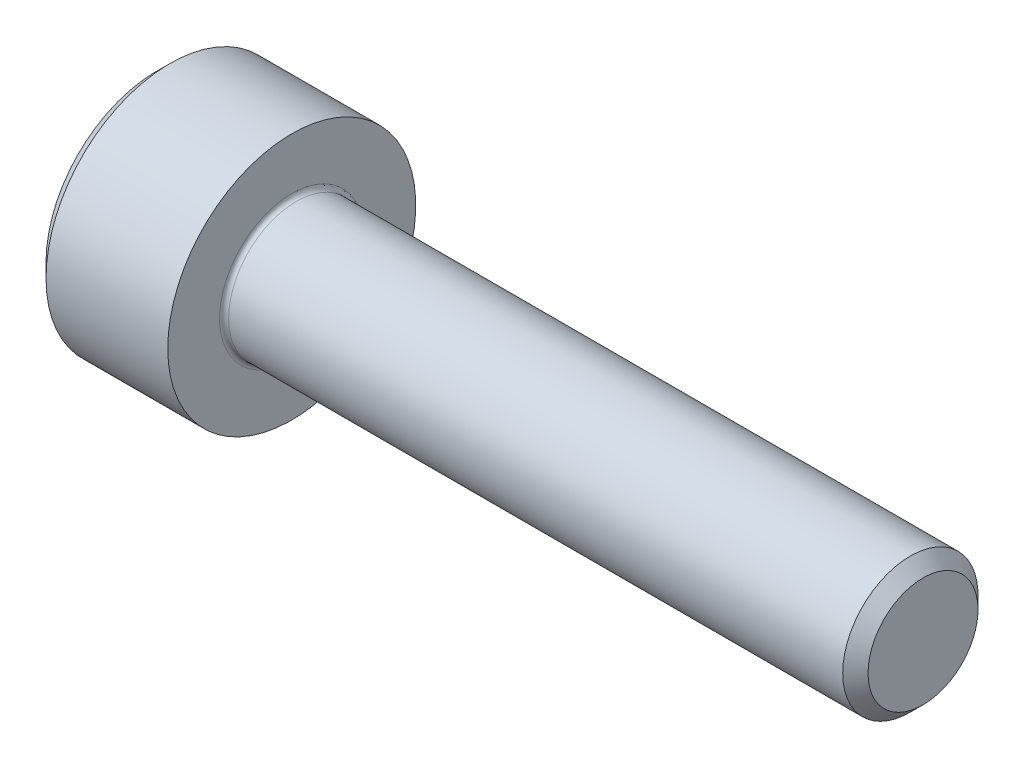
SolidWorks part; units mm, degrees
revolve "Base-Revolve" add sketch "BodySke"
sketch "BodySke" plane through (0, 0, 0) normal (0, 0, 1) x (1, 0, 0)
  line L0 (0, 0) -> (0, 2.45)
  line L1 (0.3, 2.75) -> (3, 2.75)
  line L2 (3, 2.75) -> (3, 1.5)
  line L3 (3, 1.5) -> (16.7195, 1.5)
  line L4 (17, 1.2195) -> (17, 0)
  line L5 (17, 0) -> (0, 0)
  line L6 (-31.75, 0) -> (127, 0) construction
  line L7 (0, 2.45) -> (0.3, 2.75)
  line L8 (17, 1.2195) -> (16.7195, 1.5)
  line L9 (0, -2.45) -> (0.3, -2.75) construction
  line L10 (17, -1.2195) -> (16.7195, -1.5) construction
  line L11 (3.5, 9.525) -> (3.5, 3.175) construction
  line L12 (3, 9.525) -> (3, 3.175) construction
  line L13 (-33, 9.525) -> (-33, 3.175) construction
  dimension "Diameter" = 3
  dimension "Head_ht" = 3
  dimension "Length" = 14
  dimension "Body_ch_ang" = 45
  dimension "Head_dia" = 5.5
  dimension "Head_ch_ang" = 45
  dimension "Minor_dia" = 2.439
  dimension "Advance" = 0.5
  dimension "Thread_nom" = 14
  dimension "Thread_length" = 50
  dimension "Head_ch_ht" = 0.3
cosmetic thread "ThreadCosmetic" [suppressed]
fillet "Fillet1" radius 0.1 1 edges at (3, 0, 1.5)
material "Plain Carbon Steel"
ref_plane "Plane1" through (0, 0, 0) normal (0, 0, 1) x (1, 0, 0)
ref_plane "Plane2" through (0, 0, 0) normal (0, 1, 0) x (1, 0, 0)
ref_plane "Plane3" through (0, 0, 0) normal (1, 0, 0) x (0, 0, -1)
sketch "Sketch2" plane through (0, 0, 0) normal (0, 0, 1) x (1, 0, 0)
  line L0 (0, 1.28) -> (1.3, 1.28)
  line L1 (1.3, 1.28) -> (2.039, 0)
  line L2 (-31.75, 0) -> (127, 0) construction
  line L3 (2.039, 0) -> (0, 0)
  line L4 (0, 0) -> (0, 1.28)
  line L5 (0, 2.45) -> (0, -2.45) construction
  line L6 (0, 0) -> (47.625, 0) construction
  line L7 (3, -2.75) -> (3, 2.75) construction
  dimension "D1" = 1.28
  dimension "D2" = 60
revolve "Hex-PreBroach" cut sketch "Sketch2" angle 360 about L6
sketch "Sketch3" plane through (0, 0, 0) normal (-1, 0, 0) x (0, 0.5, 0.866)
  line L0 (0.739, 1.28) -> (-0.739, 1.28)
  line L1 (-0.739, 1.28) -> (-1.478, 0)
  line L2 (0.739, 1.28) -> (1.478, 0)
  line L3 (0.739, -1.28) -> (1.478, 0)
  line L4 (0.739, -1.28) -> (-0.739, -1.28)
  line L5 (-0.739, -1.28) -> (-1.478, 0)
  dimension "D1" = 1.28
  dimension "D2" = 1.28
  dimension "Hex_size" = 2.56
extrude "Hex" cut sketch "Sketch3" against normal blind 1.3
sketch "Sketch4" plane through (0, 0, 0) normal (-1, 0, 0) x (0, 0, 1)
  line L0 (0, 0) -> (1.4605, 0)
  line L1 (0, 0) -> (6.1484, 3.5498) construction
  line L2 (0, 0) -> (0.7302, 1.2648)
  line L3 (1.2009, 0.3267) -> (1.3933, 0.4378)
  line L4 (0.8834, 0.8767) -> (1.0758, 0.9877)
  arc A0 (1.2009, 0.3267) -> (0.8834, 0.8767) centre (0, 0) ccw
  arc A1 (1.4605, 0) -> (1.3933, 0.4378) centre (0, 0) ccw
  arc A2 (0.7302, 1.2648) -> (1.0758, 0.9877) centre (0, 0) cw
  dimension "D1" = 30
  dimension "D2" = 60
  dimension "Spline_p_dim" = 0.635
  dimension "D3" = 0.3175
extrude "Spline" [suppressed] cut sketch "Sketch4" against normal blind 1.3
pattern_circular "CirPattern1" [suppressed] count 6 every 60
sketch "Sketch5" plane through (0, 0, 0) normal (0, 0, 1) x (1, 0, 0)
  line L0 (-31.75, 0) -> (127, 0) construction
  line L2 (0, 2.45) -> (0, -2.45) construction
  circle A0 centre (1.2, 0) radius 0.475
  dimension "Drilled_hole_dia" = 0.95
  dimension "Drilled_hole_loc" = 1.2
extrude "Hole" [suppressed] cut sketch "Sketch5" against normal through all and the other way through all
pattern_circular "Drilled-4" [suppressed] count 2 every 60
pattern_circular "Drilled-6" [suppressed] count 3 every 60
sketch "ThdSchSke" plane through (0, 0, 0) normal (0, 0, 1) x (1, 0, 0)
  line L0 (3.5, -1.2195) -> (3.3036, -1.5)
  line L1 (3.5, -1.2195) -> (3.6964, -1.5)
  line L2 (3.6964, -1.5) -> (3.6964, -1.875)
  line L3 (-3.175, 0) -> (5.1513, 0) construction
  line L5 (3.6964, -1.875) -> (3.3036, -1.875)
  line L6 (3.3036, -1.875) -> (3.3036, -1.5)
  line L7 (0, 2.45) -> (0, -2.45) construction
  dimension "Thread_minor" = 2.439
  dimension "Diameter" = 3
  dimension "Start" = 3.5
revolve "ThreadSchematic" [suppressed] cut sketch "ThdSchSke" angle 360 about L3
pattern_linear "ThdSchPat" [suppressed]
equation "\"D2@Sketch3\" = \"Hex_size@Sketch3\" / 2"
equation "\"D1@Sketch3\" = \"Hex_size@Sketch3\" / 2"
equation "\"D1@Sketch2\" = \"Hex_size@Sketch3\" / 2"
equation "\"D3@Sketch4\" = \"Spline_p_dim@Sketch4\" / 2"
equation "\"Thread_minor@ThreadCosmetic\"  =  \"Minor_dia@BodySke\""
equation "\"D2@CirPattern1\" = 360 / \"Num_teeth@CirPattern1\""
equation "\"Wall_thickness@Sketch2\" = \"Head_ht@BodySke\" - \"Key_eng@Hex\""
equation "\"Thread_length@ThreadCosmetic\" = ((sgn( (\"Length@BodySke\" - \"Advance@BodySke\" ) - \"Thread_nom@BodySke\" )-1)*( (\"Length@BodySke\" - \"Advance@BodySke\" ) - \"Thread_nom@BodySke\" ))/-2+ \"Thread_nom@BodySke\""
equation "\"Thread_minor@ThdSchSke\" = \"Minor_dia@BodySke\""
equation "\"Diameter@ThdSchSke\" = \"Diameter@BodySke\""
equation "\"Overcut@ThdSchSke\" = \"Diameter@BodySke\" * 1.25"
equation "\"Start@ThdSchSke\" = \"Head_ht@BodySke\" + \"Length@BodySke\" - \"Thread_length@ThreadCosmetic\"  '---Non-countersunk---"
equation "\"Num_threads@ThdSchPat\" = int( \"Thread_length@ThreadCosmetic\" / \"Advance@BodySke\" + 0.999 )  + 1"
equation "\"Advance@ThdSchPat\" = \"Thread_length@ThreadCosmetic\" /  (\"Num_threads@ThdSchPat\" - 1) 'relax it"
equation "\"Num_threads@ThdSchPat\" = \"Num_threads@ThdSchPat\" - sgn( \"Num_threads@ThdSchPat\" - 1) '---chamfered tips only---"
